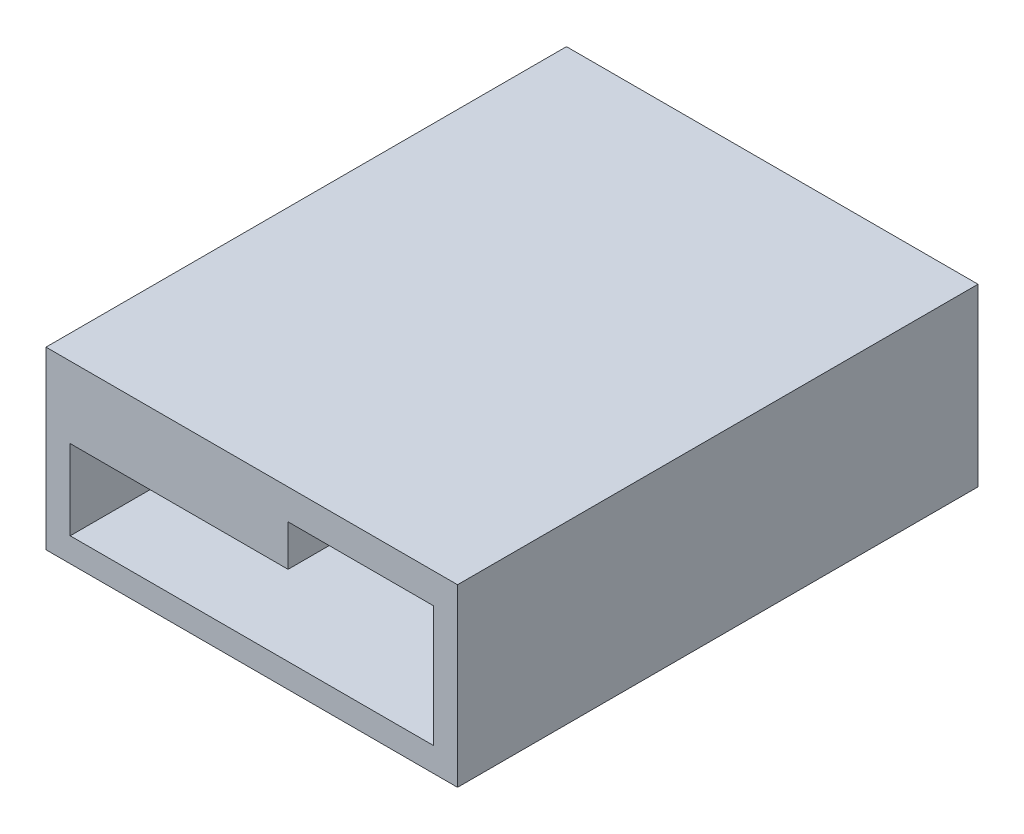
SolidWorks part; units mm, degrees
ref_plane "Front Plane" through (0, 0, 0) normal (0, 0, 1) x (1, 0, 0)
ref_plane "Top Plane" through (0, 0, 0) normal (0, 1, 0) x (1, 0, 0)
ref_plane "Right Plane" through (0, 0, 0) normal (1, 0, 0) x (0, 0, -1)
sketch "Sketch2" plane through (0, 0, 0) normal (0, 1, 0) x (1, 0, 0)
  line L0 (11, 0) -> (-11, 0)
  line L1 (-11, 0) -> (-11, 6)
  line L2 (-11, 6) -> (-15.5, 6)
  line L3 (-15.5, 6) -> (-15.5, 47)
  line L4 (-15.5, 47) -> (9.5, 47)
  line L5 (0, 0) -> (0, 47) construction
  line L6 (11, 0) -> (11, 6)
  line L7 (9.5, 47) -> (9.5, 35)
  line L8 (9.5, 35) -> (2.5, 35)
  line L9 (2.5, 35) -> (2.5, 6)
  line L10 (2.5, 6) -> (11, 6)
  dimension "D1" = 11
  dimension "D2" = 6
  dimension "D3" = 4.5
  dimension "D4" = 41
  dimension "D5" = 25
  dimension "D6" = 12
  dimension "D7" = 18
extrude "Boss-Extrude1" add sketch "Sketch2" along normal blind 0.4
sketch "Sketch3" plane through (0, 0.4, 0) normal (0, 1, 0) x (1, 0, 0)
  line L0 (-15.5, 6) -> (2.5, 6)
  line L1 (2.5, 6) -> (2.5, 35)
  line L2 (2.5, 35) -> (9.5, 35)
  line L3 (9.5, 35) -> (9.5, 47)
  line L4 (9.5, 47) -> (-15.5, 47)
  line L5 (-15.5, 47) -> (-15.5, 6)
extrude "Boss-Extrude2" add sketch "Sketch3" along normal blind 3
chamfer "Chamfer1" distance 1 angle 45 2 edges at (11, 0.2, 0) (-11, 0.2, 0)
sketch "Sketch4" plane through (0, 3.4, 0) normal (0, 1, 0) x (1, 0, 0)
  line L0 (-15.5, 6) -> (-17.5, 6) construction
  line L1 (-17.5, 6) -> (16.5, 6)
  line L2 (-17.5, 6) -> (-17.5, 49)
  line L3 (-17.5, 49) -> (16.5, 49)
  line L4 (16.5, 6) -> (16.5, 49)
  line L5 (9.5, 47) -> (-15.5, 47) construction
  line L7 (-15.5, 47) -> (-15.5, 6) construction
  dimension "D1" = 2
  dimension "D2" = 2
  dimension "D3" = 32
extrude "Boss-Extrude3" add sketch "Sketch4" along normal blind 2.5
sketch "Sketch5" plane through (0, 3.4, 0) normal (0, -1, 0) x (1, 0, 0)
  line L0 (-15.5, -6) -> (-17.5, -6)
  line L1 (-17.5, -6) -> (-17.5, -49)
  line L2 (-17.5, -49) -> (16.5, -49)
  line L3 (16.5, -49) -> (16.5, -6)
  line L4 (16.5, -6) -> (14.5, -6)
  line L5 (2.5, -6) -> (16.5, -6) construction
  line L6 (-15.5, -6) -> (-15.5, -47)
  line L7 (-15.5, -47) -> (14.5, -47)
  line L8 (14.5, -47) -> (14.5, -6)
  dimension "D1" = 2
extrude "Boss-Extrude4" add sketch "Sketch5" along normal blind 10
sketch "Sketch6" plane through (0, 0, 0) normal (0, -1, 0) x (1, 0, 0)
  line L0 (-11, -1) -> (-11, 0) construction
  line L1 (11, -6) -> (-11, -6)
  line L2 (11, -6) -> (11, 0)
  line L3 (11, 0) -> (-11, 0)
  line L4 (-11, -6) -> (-11, 0)
  point P8 (-10.6092, -0.0254)
  dimension "D1" = 6
extrude "Cut-Extrude1" cut sketch "Sketch6" against normal up to next
sketch "Sketch7" plane through (0, -6.6, 0) normal (0, -1, 0) x (1, 0, 0)
  line L1 (16.5, -49) -> (-17.5, -49)
  line L2 (16.5, -49) -> (16.5, -6)
  line L3 (16.5, -6) -> (-17.5, -6)
  line L4 (-17.5, -49) -> (-17.5, -6)
extrude "Boss-Extrude5" add sketch "Sketch7" along normal blind 2
